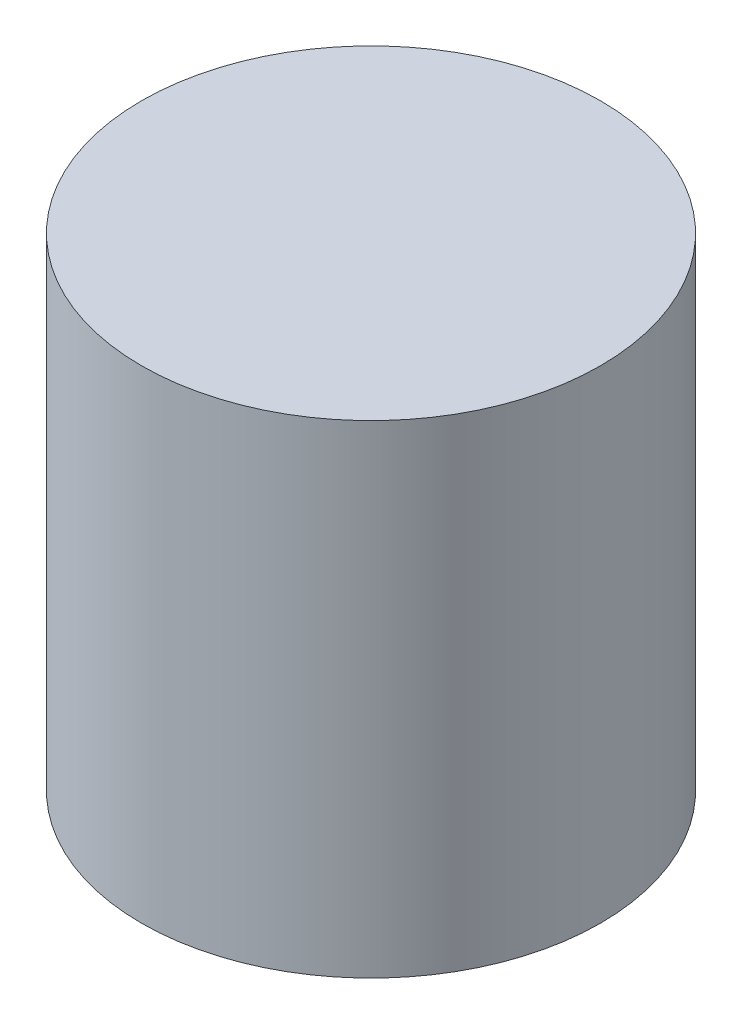
SolidWorks part; units mm, degrees
ref_plane "Front Plane" through (0, 0, 0) normal (0, 0, 1) x (1, 0, 0)
ref_plane "Top Plane" through (0, 0, 0) normal (0, 1, 0) x (1, 0, 0)
ref_plane "Right Plane" through (0, 0, 0) normal (1, 0, 0) x (0, 0, -1)
sketch "Sketch1" plane through (0, 0, 0) normal (0, 1, 0) x (1, 0, 0)
  circle A0 centre (0, 0) radius 67.5
  dimension "D1" = 135
extrude "Extrude1" add sketch "Sketch1" along normal blind 142
